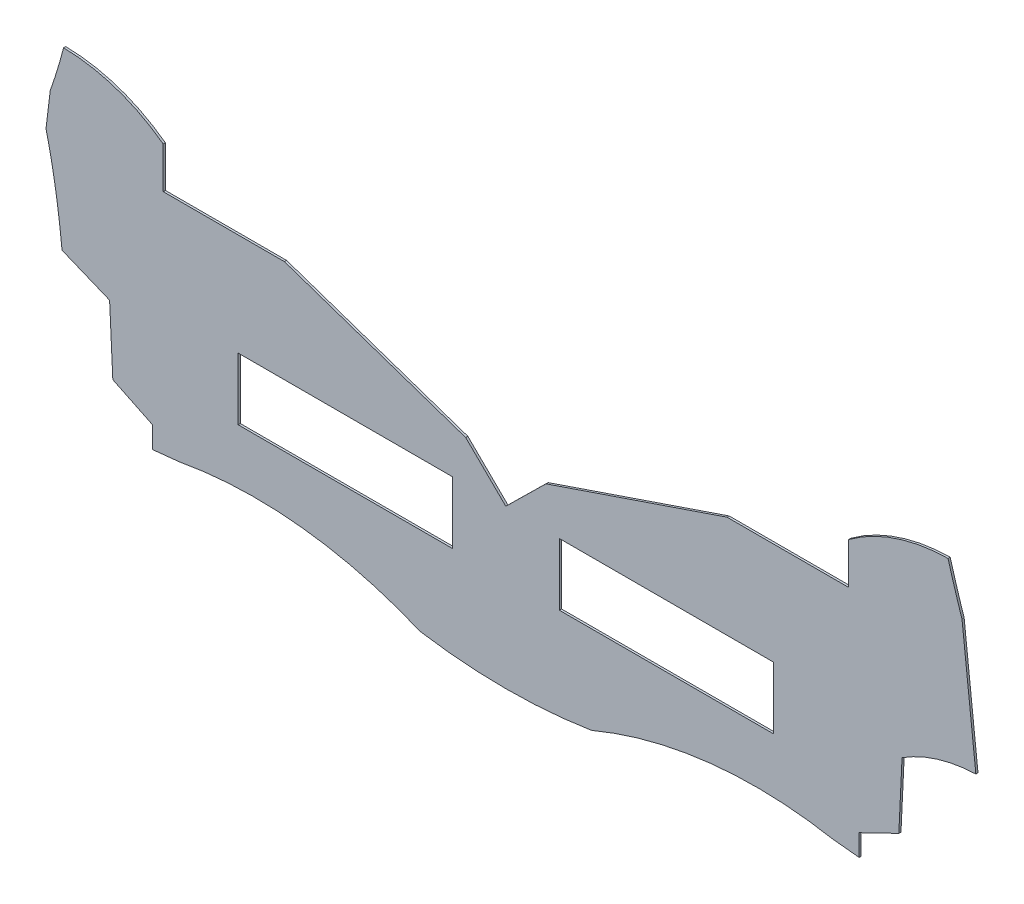
SolidWorks part; units mm, degrees
ref_plane "Alzado" through (0, 0, 0) normal (0, 0, 1) x (1, 0, 0)
ref_plane "Planta" through (0, 0, 0) normal (0, 1, 0) x (1, 0, 0)
ref_plane "Vista lateral" through (0, 0, 0) normal (1, 0, 0) x (0, 0, -1)
sketch "Model" plane through (0, 0, 0) normal (0, 0, 1) x (1, 0, 0)
  line L0 (52.4992, -23.4496) -> (51.8524, -17.5082)
  line L1 (48.9022, -27.6486) -> (49.0517, -24.5105)
  line L2 (47.0458, -28.5488) -> (48.9022, -27.6486)
  line L3 (47.0458, -29.5488) -> (47.0458, -28.5488)
  line L4 (45.8203, -29.4228) -> (47.0458, -29.5488)
  line L5 (14.0499, -29.5512) -> (15.2754, -29.425)
  line L6 (14.0498, -28.5512) -> (14.0499, -29.5512)
  line L7 (12.1932, -27.6513) -> (14.0498, -28.5512)
  line L8 (12.0434, -24.5132) -> (12.1932, -27.6513)
  line L9 (9.8201, -23.6025) -> (12.0434, -24.5132)
  line L10 (43.0471, -23.6488) -> (33.0471, -23.6488)
  line L11 (33.0471, -23.6488) -> (33.0471, -26.5488)
  line L12 (33.0471, -26.5488) -> (43.0471, -26.5488)
  line L13 (43.0471, -26.5488) -> (43.0471, -23.6488)
  line L14 (18.0471, -26.5488) -> (28.0471, -26.5488)
  line L15 (28.0471, -26.5488) -> (28.0471, -23.6488)
  line L16 (28.0471, -23.6488) -> (18.0471, -23.6488)
  line L17 (18.0471, -23.6488) -> (18.0471, -26.5488)
  line L18 (14.5471, -18.8708) -> (14.5465, -16.9424)
  line L19 (20.2117, -18.8708) -> (14.5471, -18.8708)
  line L20 (46.5471, -16.9409) -> (46.5471, -18.8708)
  line L21 (40.8791, -18.8708) -> (32.4223, -21.7502)
  line L22 (32.4223, -21.7502) -> (30.5472, -23.5942)
  line L23 (20.2117, -18.8708) -> (28.6717, -21.7504)
  line L24 (28.6717, -21.7504) -> (30.5472, -23.5942)
  line L25 (9.0935, -19.1548) -> (9.0884, -19.1336)
  line L26 (9.0987, -19.1761) -> (9.0935, -19.1548)
  line L27 (9.1038, -19.1974) -> (9.0987, -19.1761)
  line L28 (9.1089, -19.2188) -> (9.1038, -19.1974)
  line L29 (9.114, -19.2401) -> (9.1089, -19.2188)
  line L30 (9.1191, -19.2615) -> (9.114, -19.2401)
  line L31 (9.1241, -19.2829) -> (9.1191, -19.2615)
  line L32 (9.1292, -19.3044) -> (9.1241, -19.2829)
  line L33 (9.1342, -19.3258) -> (9.1292, -19.3044)
  line L34 (9.1392, -19.3473) -> (9.1342, -19.3258)
  line L35 (9.1442, -19.3688) -> (9.1392, -19.3473)
  line L36 (9.1492, -19.3904) -> (9.1442, -19.3688)
  line L37 (9.1542, -19.4119) -> (9.1492, -19.3904)
  line L38 (9.1592, -19.4335) -> (9.1542, -19.4119)
  line L39 (9.1642, -19.4551) -> (9.1592, -19.4335)
  line L40 (9.1691, -19.4768) -> (9.1642, -19.4551)
  line L41 (9.174, -19.4984) -> (9.1691, -19.4768)
  line L42 (9.1789, -19.5201) -> (9.174, -19.4984)
  line L43 (9.1839, -19.5418) -> (9.1789, -19.5201)
  line L44 (9.1887, -19.5636) -> (9.1839, -19.5418)
  line L45 (9.1936, -19.5853) -> (9.1887, -19.5636)
  line L46 (9.1985, -19.6071) -> (9.1936, -19.5853)
  line L47 (9.2033, -19.6289) -> (9.1985, -19.6071)
  line L48 (9.2082, -19.6508) -> (9.2033, -19.6289)
  line L49 (9.213, -19.6727) -> (9.2082, -19.6508)
  line L50 (9.2178, -19.6945) -> (9.213, -19.6727)
  line L51 (9.2226, -19.7165) -> (9.2178, -19.6945)
  line L52 (9.2274, -19.7384) -> (9.2226, -19.7165)
  line L53 (9.2321, -19.7604) -> (9.2274, -19.7384)
  line L54 (9.2369, -19.7824) -> (9.2321, -19.7604)
  line L55 (9.2416, -19.8044) -> (9.2369, -19.7824)
  line L56 (9.2464, -19.8264) -> (9.2416, -19.8044)
  line L57 (9.2511, -19.8485) -> (9.2464, -19.8264)
  line L58 (9.2558, -19.8706) -> (9.2511, -19.8485)
  line L59 (9.2605, -19.8927) -> (9.2558, -19.8706)
  line L60 (9.2651, -19.9149) -> (9.2605, -19.8927)
  line L61 (9.2698, -19.937) -> (9.2651, -19.9149)
  line L62 (9.2744, -19.9592) -> (9.2698, -19.937)
  line L63 (9.2791, -19.9815) -> (9.2744, -19.9592)
  line L64 (9.2837, -20.0037) -> (9.2791, -19.9815)
  line L65 (9.2883, -20.026) -> (9.2837, -20.0037)
  line L66 (9.2929, -20.0483) -> (9.2883, -20.026)
  line L67 (9.2974, -20.0706) -> (9.2929, -20.0483)
  line L68 (9.302, -20.093) -> (9.2974, -20.0706)
  line L69 (9.3066, -20.1153) -> (9.302, -20.093)
  line L70 (9.3111, -20.1377) -> (9.3066, -20.1153)
  line L71 (9.3156, -20.1602) -> (9.3111, -20.1377)
  line L72 (9.3201, -20.1826) -> (9.3156, -20.1602)
  line L73 (9.3246, -20.2051) -> (9.3201, -20.1826)
  line L74 (9.3291, -20.2276) -> (9.3246, -20.2051)
  line L75 (9.3336, -20.2501) -> (9.3291, -20.2276)
  line L76 (9.338, -20.2727) -> (9.3336, -20.2501)
  line L77 (9.3425, -20.2953) -> (9.338, -20.2727)
  line L78 (9.3469, -20.3179) -> (9.3425, -20.2953)
  line L79 (9.3513, -20.3405) -> (9.3469, -20.3179)
  line L80 (9.3557, -20.3631) -> (9.3513, -20.3405)
  line L81 (9.3601, -20.3858) -> (9.3557, -20.3631)
  line L82 (9.3645, -20.4085) -> (9.3601, -20.3858)
  line L83 (9.3688, -20.4313) -> (9.3645, -20.4085)
  line L84 (9.3732, -20.454) -> (9.3688, -20.4313)
  line L85 (9.3775, -20.4768) -> (9.3732, -20.454)
  line L86 (9.3818, -20.4996) -> (9.3775, -20.4768)
  line L87 (9.3861, -20.5224) -> (9.3818, -20.4996)
  line L88 (9.3904, -20.5453) -> (9.3861, -20.5224)
  line L89 (9.3947, -20.5682) -> (9.3904, -20.5453)
  line L90 (9.399, -20.5911) -> (9.3947, -20.5682)
  line L91 (9.4032, -20.614) -> (9.399, -20.5911)
  line L92 (9.4075, -20.637) -> (9.4032, -20.614)
  line L93 (9.4117, -20.66) -> (9.4075, -20.637)
  line L94 (9.4159, -20.683) -> (9.4117, -20.66)
  line L95 (9.4201, -20.706) -> (9.4159, -20.683)
  line L96 (9.4243, -20.7291) -> (9.4201, -20.706)
  line L97 (9.4285, -20.7522) -> (9.4243, -20.7291)
  line L98 (9.4326, -20.7753) -> (9.4285, -20.7522)
  line L99 (9.4368, -20.7984) -> (9.4326, -20.7753)
  line L100 (9.4409, -20.8216) -> (9.4368, -20.7984)
  line L101 (9.445, -20.8448) -> (9.4409, -20.8216)
  line L102 (9.4491, -20.868) -> (9.445, -20.8448)
  line L103 (9.4532, -20.8912) -> (9.4491, -20.868)
  line L104 (9.4573, -20.9145) -> (9.4532, -20.8912)
  line L105 (9.4613, -20.9378) -> (9.4573, -20.9145)
  line L106 (9.4654, -20.9611) -> (9.4613, -20.9378)
  line L107 (9.4694, -20.9844) -> (9.4654, -20.9611)
  line L108 (9.4734, -21.0078) -> (9.4694, -20.9844)
  line L109 (9.4774, -21.0312) -> (9.4734, -21.0078)
  line L110 (9.4814, -21.0546) -> (9.4774, -21.0312)
  line L111 (9.4854, -21.078) -> (9.4814, -21.0546)
  line L112 (9.4894, -21.1015) -> (9.4854, -21.078)
  line L113 (9.4933, -21.125) -> (9.4894, -21.1015)
  line L114 (9.4973, -21.1485) -> (9.4933, -21.125)
  line L115 (9.5012, -21.1721) -> (9.4973, -21.1485)
  line L116 (9.5051, -21.1956) -> (9.5012, -21.1721)
  line L117 (9.509, -21.2192) -> (9.5051, -21.1956)
  line L118 (9.5129, -21.2428) -> (9.509, -21.2192)
  line L119 (9.5168, -21.2665) -> (9.5129, -21.2428)
  line L120 (9.5206, -21.2902) -> (9.5168, -21.2665)
  line L121 (9.5245, -21.3139) -> (9.5206, -21.2902)
  line L122 (9.5283, -21.3376) -> (9.5245, -21.3139)
  line L123 (9.5321, -21.3613) -> (9.5283, -21.3376)
  line L124 (9.5359, -21.3851) -> (9.5321, -21.3613)
  line L125 (9.5397, -21.4089) -> (9.5359, -21.3851)
  line L126 (9.5435, -21.4327) -> (9.5397, -21.4089)
  line L127 (9.5472, -21.4566) -> (9.5435, -21.4327)
  line L128 (9.551, -21.4804) -> (9.5472, -21.4566)
  line L129 (9.5547, -21.5043) -> (9.551, -21.4804)
  line L130 (9.5585, -21.5283) -> (9.5547, -21.5043)
  line L131 (9.5622, -21.5522) -> (9.5585, -21.5283)
  line L132 (9.5659, -21.5762) -> (9.5622, -21.5522)
  line L133 (9.5695, -21.6002) -> (9.5659, -21.5762)
  line L134 (9.5732, -21.6242) -> (9.5695, -21.6002)
  line L135 (9.5769, -21.6483) -> (9.5732, -21.6242)
  line L136 (9.5805, -21.6723) -> (9.5769, -21.6483)
  line L137 (9.5841, -21.6964) -> (9.5805, -21.6723)
  line L138 (9.5877, -21.7206) -> (9.5841, -21.6964)
  line L139 (9.5913, -21.7447) -> (9.5877, -21.7206)
  line L140 (9.5949, -21.7689) -> (9.5913, -21.7447)
  line L141 (9.5985, -21.7931) -> (9.5949, -21.7689)
  line L142 (9.6021, -21.8173) -> (9.5985, -21.7931)
  line L143 (9.6056, -21.8416) -> (9.6021, -21.8173)
  line L144 (9.6091, -21.8659) -> (9.6056, -21.8416)
  line L145 (9.6127, -21.8902) -> (9.6091, -21.8659)
  line L146 (9.6162, -21.9145) -> (9.6127, -21.8902)
  line L147 (9.6197, -21.9389) -> (9.6162, -21.9145)
  line L148 (9.6231, -21.9632) -> (9.6197, -21.9389)
  line L149 (9.6266, -21.9876) -> (9.6231, -21.9632)
  line L150 (9.6301, -22.0121) -> (9.6266, -21.9876)
  line L151 (9.6335, -22.0365) -> (9.6301, -22.0121)
  line L152 (9.6369, -22.061) -> (9.6335, -22.0365)
  line L153 (9.6403, -22.0855) -> (9.6369, -22.061)
  line L154 (9.6437, -22.1101) -> (9.6403, -22.0855)
  line L155 (9.6471, -22.1346) -> (9.6437, -22.1101)
  line L156 (9.6505, -22.1592) -> (9.6471, -22.1346)
  line L157 (9.6538, -22.1838) -> (9.6505, -22.1592)
  line L158 (9.6572, -22.2085) -> (9.6538, -22.1838)
  line L159 (9.6605, -22.2331) -> (9.6572, -22.2085)
  line L160 (9.6638, -22.2578) -> (9.6605, -22.2331)
  line L161 (9.6671, -22.2825) -> (9.6638, -22.2578)
  line L162 (9.6704, -22.3072) -> (9.6671, -22.2825)
  line L163 (9.6737, -22.332) -> (9.6704, -22.3072)
  line L164 (9.6769, -22.3568) -> (9.6737, -22.332)
  line L165 (9.6802, -22.3816) -> (9.6769, -22.3568)
  line L166 (9.6834, -22.4064) -> (9.6802, -22.3816)
  line L167 (9.6866, -22.4313) -> (9.6834, -22.4064)
  line L168 (9.6899, -22.4562) -> (9.6866, -22.4313)
  line L169 (9.693, -22.4811) -> (9.6899, -22.4562)
  line L170 (9.6962, -22.5061) -> (9.693, -22.4811)
  line L171 (9.6994, -22.531) -> (9.6962, -22.5061)
  line L172 (9.7025, -22.556) -> (9.6994, -22.531)
  line L173 (9.7057, -22.581) -> (9.7025, -22.556)
  line L174 (9.7088, -22.6061) -> (9.7057, -22.581)
  line L175 (9.7119, -22.6311) -> (9.7088, -22.6061)
  line L176 (9.715, -22.6562) -> (9.7119, -22.6311)
  line L177 (9.7181, -22.6814) -> (9.715, -22.6562)
  line L178 (9.7212, -22.7065) -> (9.7181, -22.6814)
  line L179 (9.7242, -22.7317) -> (9.7212, -22.7065)
  line L180 (9.7273, -22.7569) -> (9.7242, -22.7317)
  line L181 (9.7303, -22.7821) -> (9.7273, -22.7569)
  line L182 (9.7333, -22.8073) -> (9.7303, -22.7821)
  line L183 (9.7363, -22.8326) -> (9.7333, -22.8073)
  line L184 (9.7393, -22.8579) -> (9.7363, -22.8326)
  line L185 (9.7423, -22.8832) -> (9.7393, -22.8579)
  line L186 (9.7453, -22.9086) -> (9.7423, -22.8832)
  line L187 (9.7482, -22.9339) -> (9.7453, -22.9086)
  line L188 (9.7511, -22.9593) -> (9.7482, -22.9339)
  line L189 (9.7541, -22.9847) -> (9.7511, -22.9593)
  line L190 (9.757, -23.0102) -> (9.7541, -22.9847)
  line L191 (9.7599, -23.0357) -> (9.757, -23.0102)
  line L192 (9.7627, -23.0612) -> (9.7599, -23.0357)
  line L193 (9.7656, -23.0867) -> (9.7627, -23.0612)
  line L194 (9.7685, -23.1122) -> (9.7656, -23.0867)
  line L195 (9.7713, -23.1378) -> (9.7685, -23.1122)
  line L196 (9.7741, -23.1634) -> (9.7713, -23.1378)
  line L197 (9.7769, -23.189) -> (9.7741, -23.1634)
  line L198 (9.7797, -23.2147) -> (9.7769, -23.189)
  line L199 (9.7825, -23.2404) -> (9.7797, -23.2147)
  line L200 (9.7853, -23.2661) -> (9.7825, -23.2404)
  line L201 (9.7881, -23.2918) -> (9.7853, -23.2661)
  line L202 (9.7908, -23.3176) -> (9.7881, -23.2918)
  line L203 (9.7935, -23.3433) -> (9.7908, -23.3176)
  line L204 (9.7963, -23.3691) -> (9.7935, -23.3433)
  line L205 (9.799, -23.395) -> (9.7963, -23.3691)
  line L206 (9.8017, -23.4208) -> (9.799, -23.395)
  line L207 (9.8043, -23.4467) -> (9.8017, -23.4208)
  line L208 (9.807, -23.4726) -> (9.8043, -23.4467)
  line L209 (9.8096, -23.4985) -> (9.807, -23.4726)
  line L210 (9.8123, -23.5245) -> (9.8096, -23.4985)
  line L211 (9.8149, -23.5505) -> (9.8123, -23.5245)
  line L212 (9.8175, -23.5765) -> (9.8149, -23.5505)
  line L213 (9.8201, -23.6025) -> (9.8175, -23.5765)
  line L214 (9.078, -19.0911) -> (9.0729, -19.07)
  line L215 (9.0832, -19.1124) -> (9.078, -19.0911)
  line L216 (9.0884, -19.1336) -> (9.0832, -19.1124)
  line L217 (9.0729, -19.07) -> (9.2695, -17.4245)
  line L218 (40.8791, -18.8708) -> (46.5471, -18.8708)
  arc A0 (26.5442, -30.6581) -> (15.2754, -29.425) centre (18.8517, -48.8498) ccw
  arc A1 (45.8203, -29.4228) -> (34.5517, -30.6576) centre (42.2469, -48.8481) ccw
  arc A2 (51.1997, -15.3783) -> (46.5471, -16.9409) centre (51.2949, -23.3697) ccw
  arc A3 (14.5465, -16.9424) -> (9.8937, -15.3802) centre (9.7992, -23.3716) ccw
  arc A4 (51.1997, -15.3783) -> (51.8524, -17.5082) centre (98.8956, -1.9267) ccw
  arc A5 (52.4992, -23.4496) -> (49.0517, -24.5105) centre (52.72, -30.2991) ccw
  arc A6 (26.5442, -30.6581) -> (34.5517, -30.6576) centre (30.5461, -5.5275) ccw
  arc A7 (9.2695, -17.4245) -> (9.8937, -15.3802) centre (-12.9638, -9.5173) ccw
extrude "Saliente-Extruir1" add sketch "Model" along normal blind 0.1
